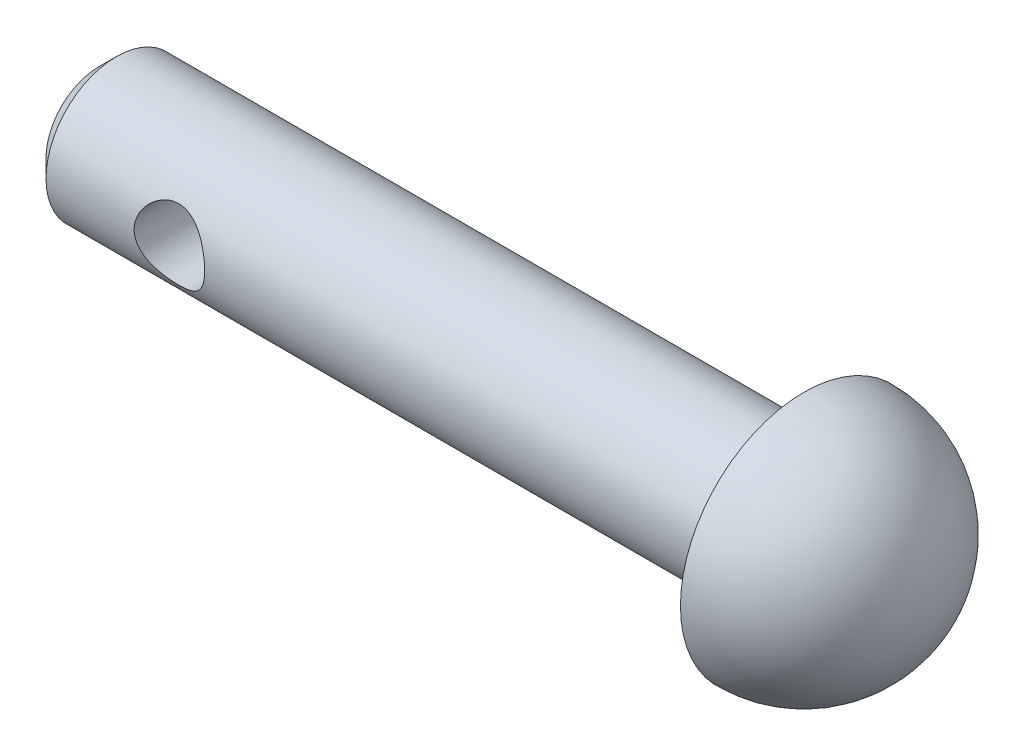
SolidWorks part; units mm, degrees
ref_plane "Front Plane" through (0, 0, 0) normal (0, 0, 1) x (1, 0, 0)
ref_plane "Top Plane" through (0, 0, 0) normal (0, 1, 0) x (1, 0, 0)
ref_plane "Right Plane" through (0, 0, 0) normal (1, 0, 0) x (0, 0, -1)
sketch "Sketch3" plane through (0, 0, 0) normal (0, 0, 1) x (1, 0, 0)
  line L0 (-20, 0) -> (-20, 2)
  line L1 (-20, 2) -> (0, 2)
  line L2 (0, 2) -> (0, 3.5)
  line L3 (-20, 0) -> (3.5, 0)
  arc A0 (3.5, 0) -> (0, 3.5) centre (0, 0) ccw
  dimension "D1" = 3.5
  dimension "D2" = 23.5
  dimension "D3" = 2
revolve "Revolve1" add sketch "Sketch3" angle 360 about L3
sketch "Sketch4" plane through (0, 0, 0) normal (0, 0, 1) x (1, 0, 0)
  line L0 (0, 2) -> (0, -2) construction
  circle A0 centre (-16, 0) radius 1
  dimension "D1" = 2
  dimension "D2" = 16
extrude "Cut-Extrude1" cut sketch "Sketch4" against normal through all both and the other way through all
chamfer "Chamfer1" distance 0.5 angle 45 1 edges at (-20, 0, 2)
